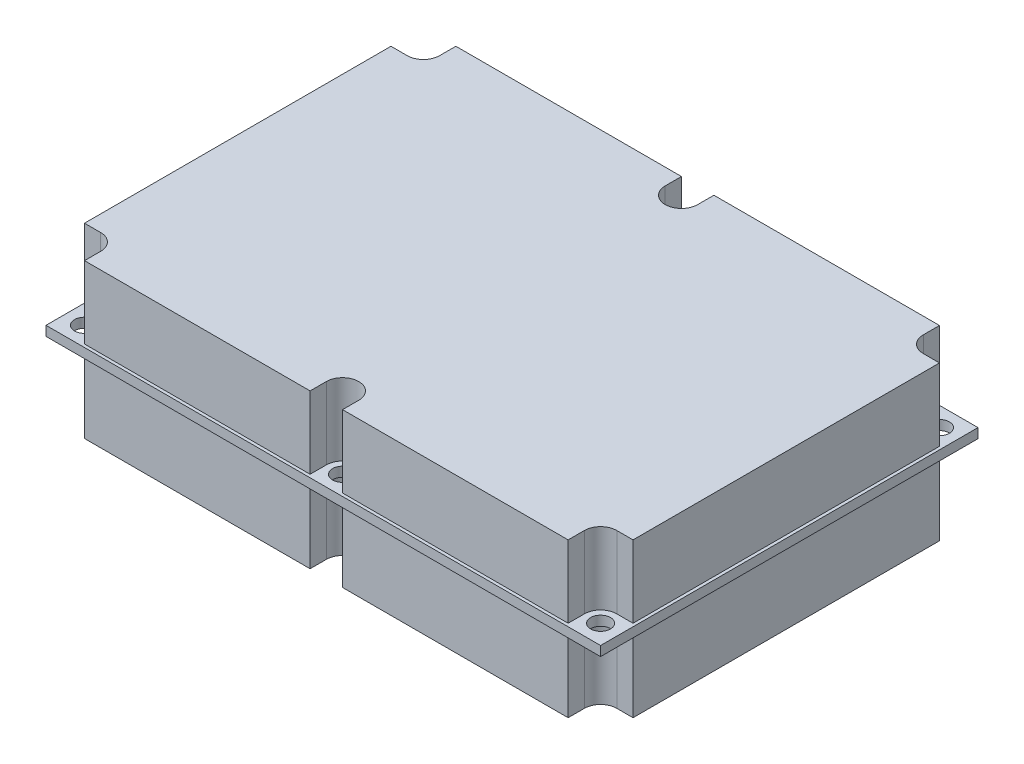
SolidWorks part; units mm, degrees
ref_plane "Front Plane" through (0, 0, 0) normal (0, 0, 1) x (1, 0, 0)
ref_plane "Top Plane" through (0, 0, 0) normal (0, 1, 0) x (1, 0, 0)
ref_plane "Right Plane" through (0, 0, 0) normal (1, 0, 0) x (0, 0, -1)
sketch "Sketch1" plane through (0, 0, 0) normal (0, 1, 0) x (1, 0, 0)
  line L1 (-45.72, 31.115) -> (45.72, 31.115)
  line L2 (-45.72, 31.115) -> (-45.72, -31.115)
  line L3 (-45.72, -31.115) -> (45.72, -31.115)
  line L4 (45.72, 31.115) -> (45.72, -31.115)
  point P4 (0, 31.115)
  point P6 (-45.72, 0)
  dimension "D1" = 62.23
  dimension "D2" = 91.44
extrude "Boss-Extrude1" add sketch "Sketch1" along normal mid plane 1.5875
sketch "Sketch3" plane through (0, 0, 0) normal (0, 1, 0) x (1, 0, 0)
  circle A0 centre (-42.545, 27.94) radius 1.6383
  dimension "D3" = 3.2766
  dimension "D1" = 27.94
  dimension "D2" = 42.545
extrude "Cut-Extrude1" cut sketch "Sketch3" against normal through all and the other way through all
pattern_linear "LPattern1" count 3 spacing 42.545 along (1, 0, 0) count 2 spacing 55.88 along (0, 0, 1) of "Cut-Extrude1"
sketch "Sketch2" plane through (0, 0, 0) normal (0, 1, 0) x (1, 0, 0)
  line L0 (-42.545, 25.265) -> (-45.22, 25.265)
  line L1 (-39.87, 27.94) -> (-39.87, 30.615)
  line L2 (-2.675, 27.94) -> (-2.675, 30.615)
  line L3 (2.675, 27.94) -> (2.675, 30.615)
  line L4 (39.87, 27.94) -> (39.87, 30.615)
  line L5 (42.545, 25.265) -> (45.22, 25.265)
  line L6 (-2.675, 30.615) -> (-39.87, 30.615)
  line L7 (39.87, 30.615) -> (2.675, 30.615)
  line L8 (-45.22, 30.615) -> (-45.22, -30.615)
  line L9 (-45.22, -30.615) -> (45.22, -30.615)
  line L10 (45.22, -30.615) -> (45.22, 30.615)
  line L11 (45.22, 30.615) -> (-45.22, 30.615)
  line L12 (-45.22, 25.265) -> (-45.22, -25.265)
  line L13 (-39.87, -30.615) -> (-2.675, -30.615)
  line L14 (45.22, -25.265) -> (45.22, 25.265)
  line L15 (45.72, 31.115) -> (-45.72, 31.115) construction
  line L16 (-42.545, -25.265) -> (-45.22, -25.265)
  line L17 (-39.87, -27.94) -> (-39.87, -30.615)
  line L18 (-2.675, -27.94) -> (-2.675, -30.615)
  line L19 (2.675, -27.94) -> (2.675, -30.615)
  line L20 (39.87, -27.94) -> (39.87, -30.615)
  line L21 (42.545, -25.265) -> (45.22, -25.265)
  line L22 (2.675, -30.615) -> (39.87, -30.615)
  arc A0 (-42.545, 25.265) -> (-39.87, 27.94) centre (-42.545, 27.94) ccw
  arc A1 (-2.675, 27.94) -> (2.675, 27.94) centre (0, 27.94) ccw
  arc A2 (39.87, 27.94) -> (42.545, 25.265) centre (42.545, 27.94) ccw
  arc A3 (-39.87, -27.94) -> (-42.545, -25.265) centre (-42.545, -27.94) ccw
  arc A4 (2.675, -27.94) -> (-2.675, -27.94) centre (0, -27.94) ccw
  arc A5 (42.545, -25.265) -> (39.87, -27.94) centre (42.545, -27.94) ccw
  dimension "D2" = 0.5
  dimension "D1" = 0.5
extrude "Boss-Extrude2" add sketch "Sketch2" along normal mid plane 25.4 separate body
